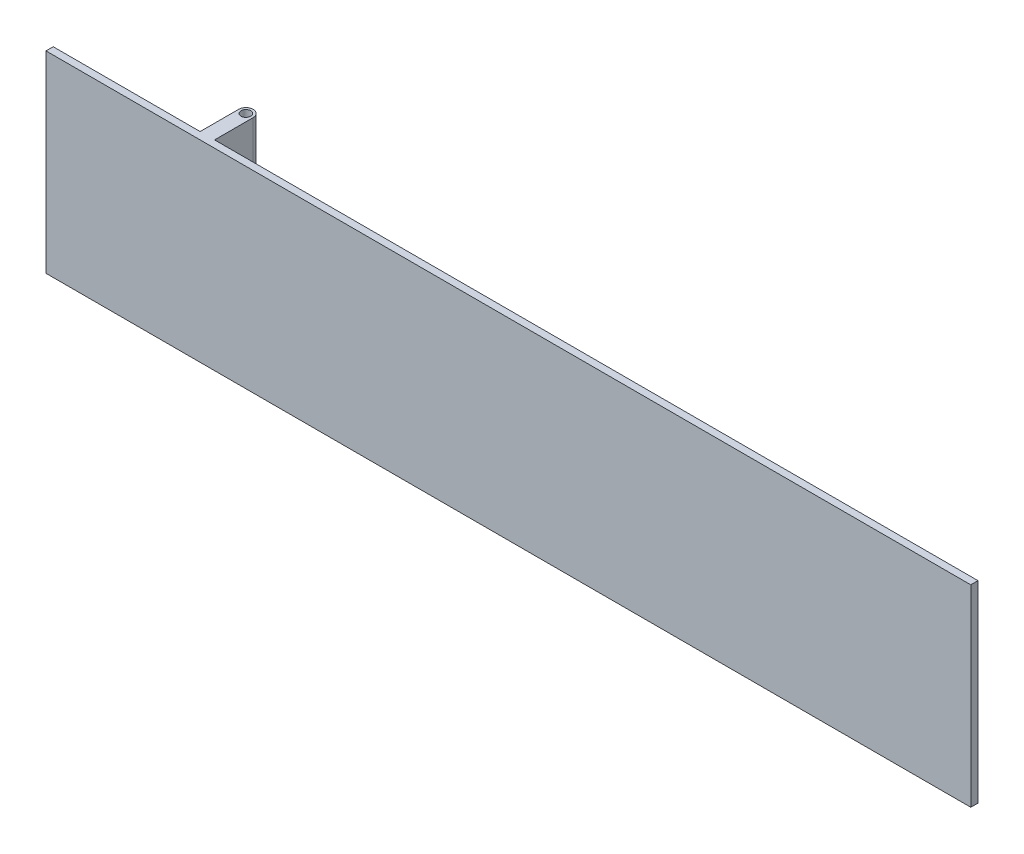
SolidWorks part; units mm, degrees
ref_plane "Front Plane" through (0, 0, 0) normal (0, 0, 1) x (1, 0, 0)
ref_plane "Top Plane" through (0, 0, 0) normal (0, 1, 0) x (1, 0, 0)
ref_plane "Right Plane" through (0, 0, 0) normal (1, 0, 0) x (0, 0, -1)
sketch "Sketch1" plane through (0, 0, 0) normal (0, 0, 1) x (1, 0, 0)
  line L1 (-304.8, -63.5) -> (304.8, -63.5)
  line L2 (-304.8, -63.5) -> (-304.8, 63.5)
  line L3 (-304.8, 63.5) -> (304.8, 63.5)
  line L4 (304.8, -63.5) -> (304.8, 63.5)
  line L5 (-304.8, -63.5) -> (304.8, 63.5) construction
  line L6 (-304.8, 63.5) -> (304.8, -63.5) construction
  point P0 (0, 0)
  dimension "D1" = 127
  dimension "D2" = 609.6
extrude "Boss-Extrude2" add sketch "Sketch1" along normal blind 4.7625 contours L3 L4 L1 L2
sketch "Sketch3" plane through (0, 0, 0) normal (0, 1, 0) x (1, 0, 0)
  line L0 (-207.9625, 0) -> (-207.9625, 25.4)
  line L1 (-304.8, 0) -> (304.8, 0) construction
  line L2 (-198.4375, 25.4) -> (-198.4375, 0)
  line L3 (-203.2, 30.1625) -> (-203.2, 0) construction
  line L4 (-304.8, -4.7625) -> (-304.8, 0) construction
  line L5 (-207.9625, 0) -> (-198.4375, 0)
  arc A0 (-207.9625, 25.4) -> (-198.4375, 25.4) centre (-203.2, 25.4) cw
  circle A1 centre (-203.2, 25.4) radius 3.175
  dimension "D1" = 4.7625
  dimension "D3" = 6.35
  dimension "D2" = 25.4
  dimension "D4" = 101.6
extrude "Boss-Extrude3" add sketch "Sketch3" along normal mid plane 127
sketch "Sketch4" plane through (-198.4375, 0, 0) normal (1, 0, 0) x (0, 0, -1)
  line L0 (0, 0) -> (30.1625, 0) construction
  line L1 (30.1625, -63.5) -> (30.1625, 63.5) construction
  line L2 (0, 25.4) -> (30.1625, 25.4)
  line L3 (0, 63.5) -> (0, -63.5) construction
  line L4 (30.1625, 25.4) -> (30.1625, -25.4)
  line L5 (30.1625, -25.4) -> (0, -25.4)
  line L6 (0, -63.5) -> (0, 63.5) construction
  line L7 (0, -25.4) -> (0, 25.4)
  dimension "D1" = 50.8
extrude "Cut-Extrude1" cut sketch "Sketch4" against normal through all
